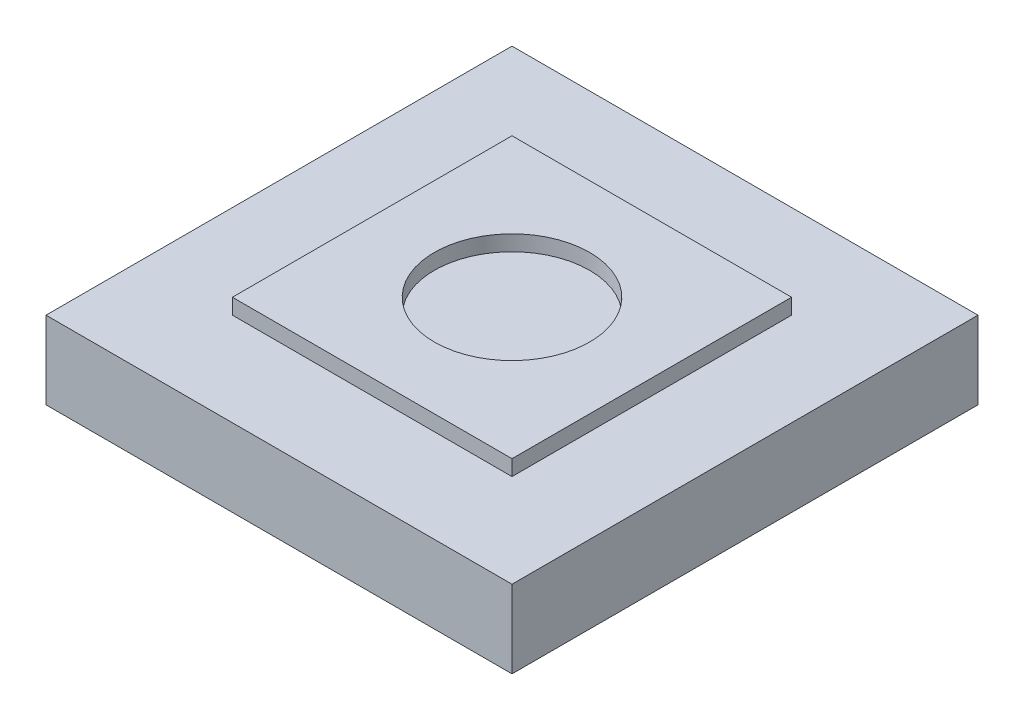
SolidWorks part; units mm, degrees
ref_plane "Front Plane" through (0, 0, 0) normal (0, 0, 1) x (1, 0, 0)
ref_plane "Top Plane" through (0, 0, 0) normal (0, 1, 0) x (1, 0, 0)
ref_plane "Right Plane" through (0, 0, 0) normal (1, 0, 0) x (0, 0, -1)
sketch "Sketch1" plane through (0, 0, 0) normal (0, 1, 0) x (1, 0, 0)
  line L1 (0, 0) -> (15.24, 0)
  line L2 (0, 0) -> (0, 15.24)
  line L3 (0, 15.24) -> (15.24, 15.24)
  line L4 (15.24, 0) -> (15.24, 15.24)
extrude "Boss-Extrude1" add sketch "Sketch1" along normal blind 2.54
sketch "Sketch2" plane through (0, 0, 0) normal (0, 1, 0) x (1, 0, 0)
  line L1 (3.048, 12.192) -> (12.192, 12.192)
  line L2 (3.048, 12.192) -> (3.048, 3.048)
  line L3 (3.048, 3.048) -> (12.192, 3.048)
  line L4 (12.192, 12.192) -> (12.192, 3.048)
extrude "Boss-Extrude2" add sketch "Sketch2" along normal blind 3.048
sketch "Sketch3" plane through (0, 3.048, 0) normal (0, 1, 0) x (1, 0, 0)
  circle A0 centre (7.62, 7.62) radius 2.54
extrude "Cut-Extrude1" cut sketch "Sketch3" against normal blind 0.508
